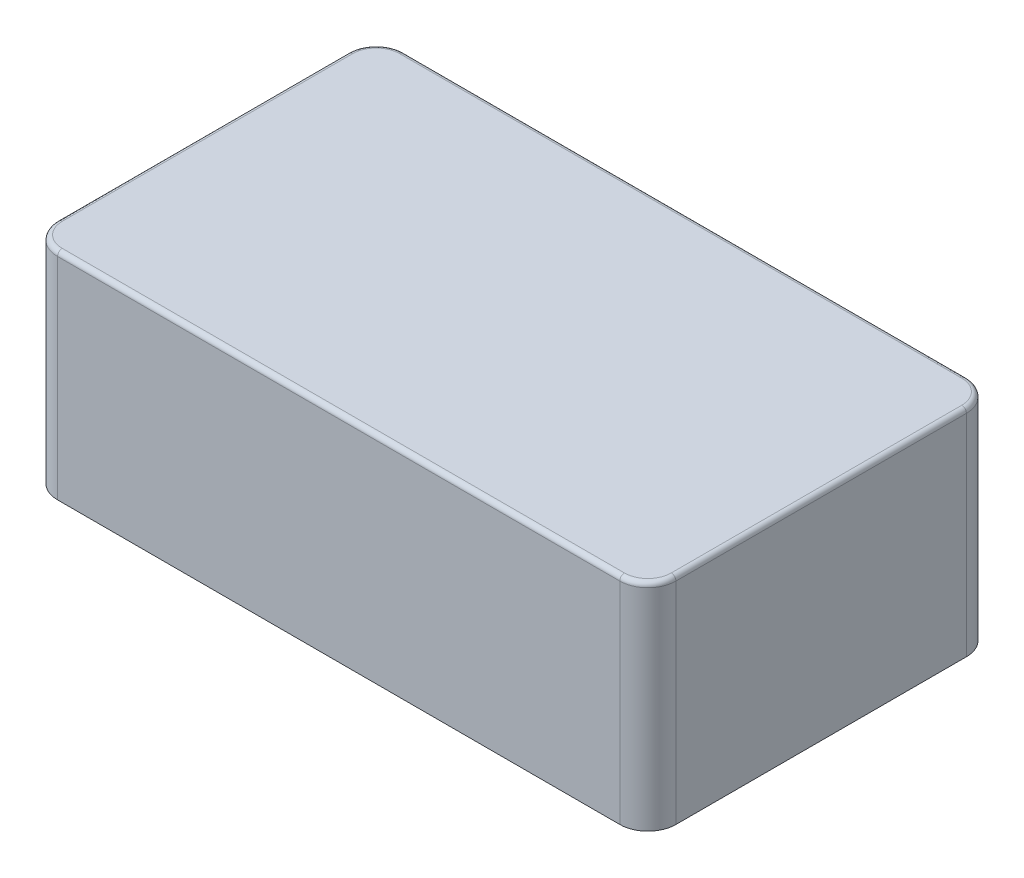
SolidWorks part; units mm, degrees
ref_plane "Front Plane" through (0, 0, 0) normal (0, 0, 1) x (1, 0, 0)
ref_plane "Top Plane" through (0, 0, 0) normal (0, 1, 0) x (1, 0, 0)
ref_plane "Right Plane" through (0, 0, 0) normal (1, 0, 0) x (0, 0, -1)
sketch "Sketch1" plane through (0, 0, 0) normal (0, 1, 0) x (1, 0, 0)
  line L1 (-28, 16.5) -> (28, 16.5)
  line L2 (-31, 13.5) -> (-31, -13.5)
  line L3 (-28, -16.5) -> (28, -16.5)
  line L4 (31, 13.5) -> (31, -13.5)
  line L5 (-31, 16.5) -> (31, -16.5) construction
  line L6 (-31, -16.5) -> (31, 16.5) construction
  line L7 (-30, 18.5) -> (30, 18.5)
  line L8 (-33, 15.5) -> (-33, -15.5)
  line L9 (-30, -18.5) -> (30, -18.5)
  line L10 (33, 15.5) -> (33, -15.5)
  line L11 (-33, 18.5) -> (33, -18.5) construction
  line L12 (-33, -18.5) -> (33, 18.5) construction
  arc A0 (31, 13.5) -> (28, 16.5) centre (28, 13.5) ccw
  arc A1 (28, -16.5) -> (31, -13.5) centre (28, -13.5) ccw
  arc A2 (-28, -16.5) -> (-31, -13.5) centre (-28, -13.5) cw
  arc A3 (-31, 13.5) -> (-28, 16.5) centre (-28, 13.5) cw
  arc A4 (30, 18.5) -> (33, 15.5) centre (30, 15.5) cw
  arc A5 (30, -18.5) -> (33, -15.5) centre (30, -15.5) ccw
  arc A6 (-30, -18.5) -> (-33, -15.5) centre (-30, -15.5) cw
  arc A7 (-33, 15.5) -> (-30, 18.5) centre (-30, 15.5) cw
  point P0 (0, 0)
  point P18 (0, 0)
  dimension "D3" = 3
  dimension "D6" = 3
  dimension "D1" = 62
  dimension "D2" = 33
  dimension "D4" = 37
  dimension "D5" = 66
extrude "Boss-Extrude1" add sketch "Sketch1" along normal blind 21
sketch "Sketch2" plane through (0, 21, 0) normal (0, 1, 0) x (1, 0, 0)
  line L1 (-30, 18.5) -> (30, 18.5)
  line L2 (-33, 15.5) -> (-33, -15.5)
  line L3 (-30, -18.5) -> (30, -18.5)
  line L4 (33, 15.5) -> (33, -15.5)
  line L5 (-33, 18.5) -> (33, -18.5) construction
  line L6 (-33, -18.5) -> (33, 18.5) construction
  arc A0 (-33, -15.5) -> (-30, -18.5) centre (-30, -15.5) ccw
  arc A1 (30, -18.5) -> (33, -15.5) centre (30, -15.5) ccw
  arc A2 (33, 15.5) -> (30, 18.5) centre (30, 15.5) ccw
  arc A3 (-33, 15.5) -> (-30, 18.5) centre (-30, 15.5) cw
  point P0 (0, 0)
  dimension "D3" = 3
  dimension "D1" = 66
  dimension "D2" = 37
extrude "Boss-Extrude2" add sketch "Sketch2" along normal blind 2
fillet "Fillet1" radius 0.5 8 edges at (-33, 23, 0) (-32.1213, 23, -17.6213) (0, 23, -18.5) (32.1213, 23, -17.6213) (33, 23, 0) (32.1213, 23, 17.6213) (0, 23, 18.5) (-32.1213, 23, 17.6213)
